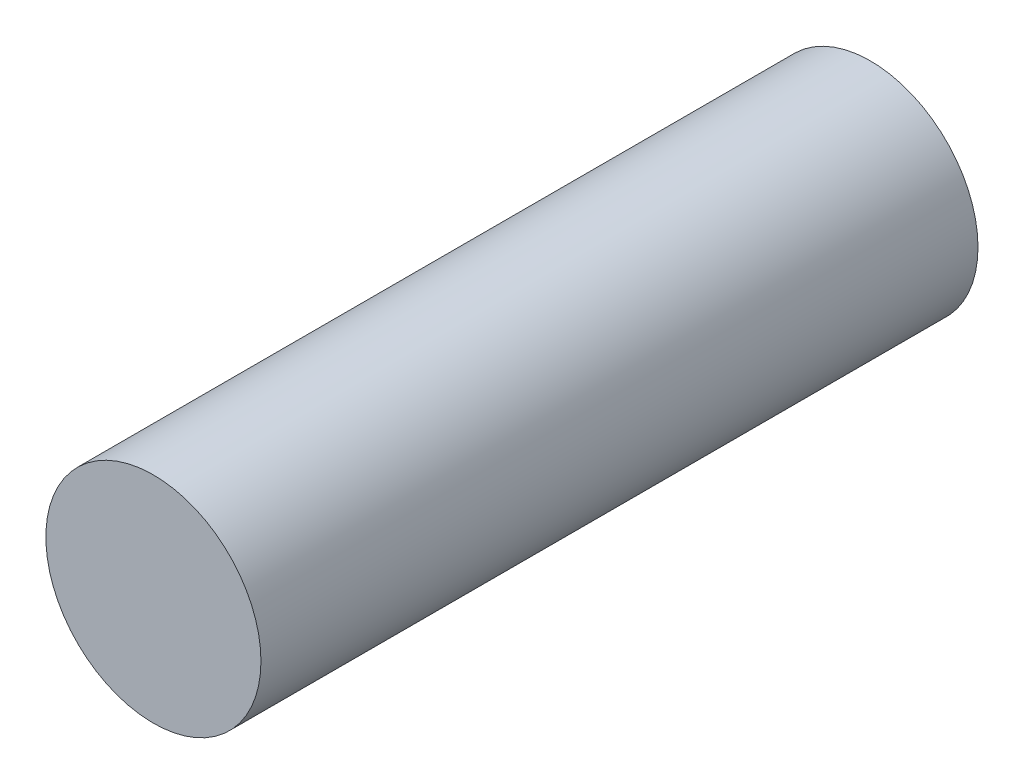
SolidWorks part; units mm, degrees
ref_plane "Front Plane" through (0, 0, 0) normal (0, 0, 1) x (1, 0, 0)
ref_plane "Top Plane" through (0, 0, 0) normal (0, 1, 0) x (1, 0, 0)
ref_plane "Right Plane" through (0, 0, 0) normal (1, 0, 0) x (0, 0, -1)
sketch "Sketch1" plane through (0, 0, 0) normal (0, 0, 1) x (1, 0, 0)
  circle A0 centre (0, 0) radius 0.15
  dimension "D1" = 0.3
extrude "Boss-Extrude1" add sketch "Sketch1" along normal blind 1
